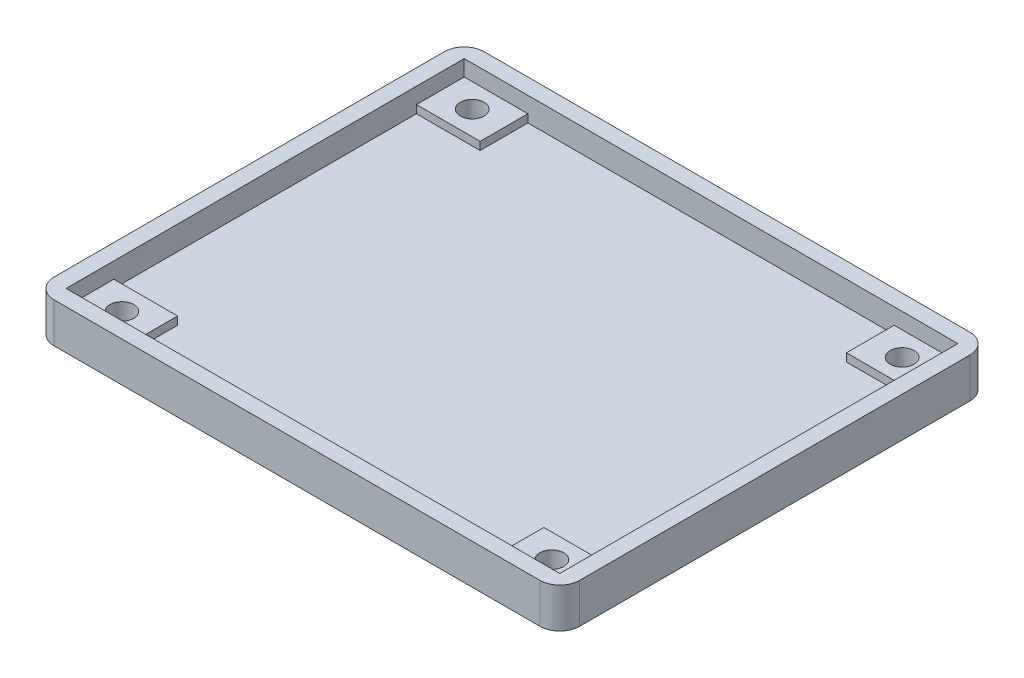
SolidWorks part; units mm, degrees
ref_plane "Front Plane" through (0, 0, 0) normal (0, 0, 1) x (1, 0, 0)
ref_plane "Top Plane" through (0, 0, 0) normal (0, 1, 0) x (1, 0, 0)
ref_plane "Right Plane" through (0, 0, 0) normal (1, 0, 0) x (0, 0, -1)
sketch "Sketch1" plane through (0, 0, 0) normal (0, 1, 0) x (1, 0, 0)
  line L1 (-33, -27) -> (33, -27)
  line L2 (-33, -27) -> (-33, 27)
  line L3 (-33, 27) -> (33, 27)
  line L4 (33, -27) -> (33, 27)
  line L5 (-33, -27) -> (33, 27) construction
  line L6 (-33, 27) -> (33, -27) construction
  point P0 (0, 0)
  dimension "D1" = 66
  dimension "D2" = 54
extrude "Boss-Extrude1" add sketch "Sketch1" along normal blind 5
sketch "Sketch2" plane through (0, 5, 0) normal (0, 1, 0) x (1, 0, 0)
  line L1 (-31, -25) -> (31, -25)
  line L2 (-31, -25) -> (-31, 25)
  line L3 (-31, 25) -> (31, 25)
  line L4 (31, -25) -> (31, 25)
  line L5 (-31, -25) -> (31, 25) construction
  line L6 (-31, 25) -> (31, -25) construction
  point P0 (0, 0)
  dimension "D1" = 62
  dimension "D2" = 50
extrude "Cut-Extrude1" cut sketch "Sketch2" against normal blind 3
sketch "Sketch3" plane through (0, 0, 0) normal (0, 1, 0) x (1, 0, 0)
  line L2 (-31, 25) -> (-31, -25) construction
  line L3 (31, 25) -> (-31, 25) construction
  line L4 (-2.75, 0) -> (2.75, 0) construction
  line L5 (0, -2.75) -> (0, 2.75) construction
  line L6 (-23, -25) -> (-23, -19)
  line L7 (-31, 25) -> (-23, 25)
  line L8 (-31, 25) -> (-31, 19)
  line L9 (-31, 19) -> (-23, 19)
  line L10 (-23, 25) -> (-23, 19)
  line L11 (-31, -25) -> (-23, -25)
  line L12 (-31, -25) -> (-31, -19)
  line L13 (-31, -19) -> (-23, -19)
  line L14 (31, -25) -> (31, -19)
  line L15 (31, -25) -> (23, -25)
  line L16 (31, -19) -> (23, -19)
  line L17 (23, -25) -> (23, -19)
  line L18 (31, 25) -> (31, 19)
  line L19 (31, 19) -> (23, 19)
  line L20 (23, 25) -> (23, 19)
  line L21 (31, 25) -> (23, 25)
  circle A0 centre (-27, 22) radius 1.5
  circle A1 centre (-27, -22) radius 1.5
  circle A2 centre (27, 22) radius 1.5
  circle A3 centre (27, -22) radius 1.5
  dimension "D1" = 3
  dimension "D2" = 4
  dimension "D3" = 3
  dimension "D4" = 6
  dimension "D5" = 8
extrude "Boss-Extrude2" add sketch "Sketch3" along normal blind 3
sketch "Sketch4" plane through (0, 2, 0) normal (0, 1, 0) x (1, 0, 0)
  circle A0 centre (-27, 22) radius 1.5
  circle A1 centre (-27, -22) radius 1.5
  circle A2 centre (27, -22) radius 1.5
  circle A3 centre (27, 22) radius 1.5
extrude "Cut-Extrude2" cut sketch "Sketch4" against normal blind 3
fillet "Fillet1" radius 2.5 4 edges at (33, 2.5, 27) (33, 2.5, -27) (-33, 2.5, 27) (-33, 2.5, -27)
